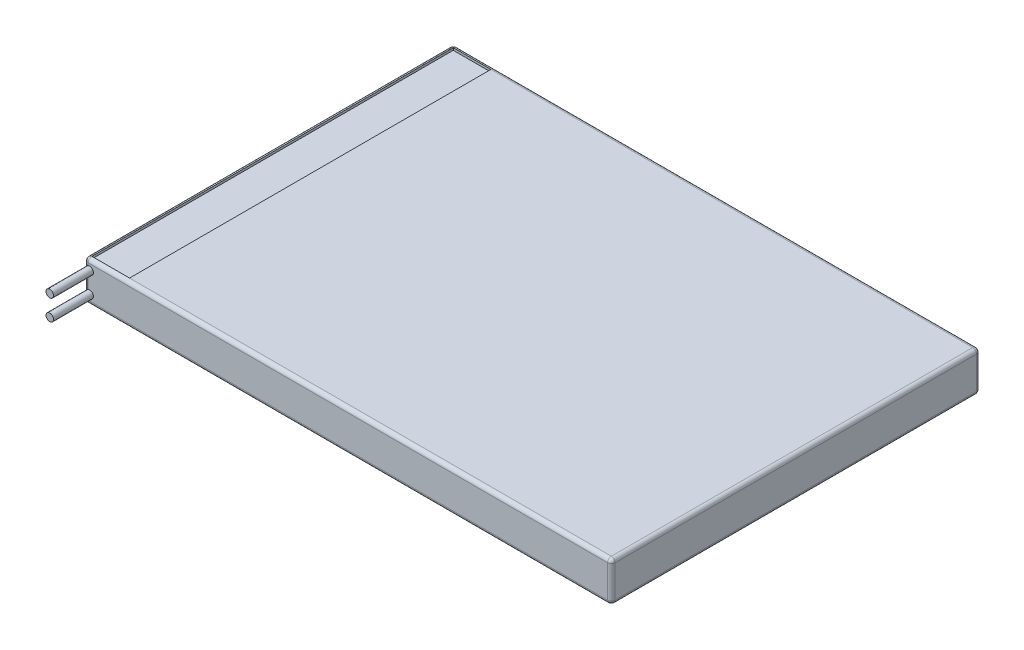
SolidWorks part; units mm, degrees
ref_plane "Front Plane" through (0, 0, 0) normal (0, 0, 1) x (1, 0, 0)
ref_plane "Top Plane" through (0, 0, 0) normal (0, 1, 0) x (1, 0, 0)
ref_plane "Right Plane" through (0, 0, 0) normal (1, 0, 0) x (0, 0, -1)
sketch "Sketch1" plane through (0, 0, 0) normal (0, 1, 0) x (1, 0, 0)
  line L1 (-34.5, -24.5) -> (34.5, -24.5)
  line L2 (-35, -24) -> (-35, 24)
  line L3 (-34.5, 24.5) -> (34.5, 24.5)
  line L4 (35, -24) -> (35, 24)
  line L5 (-35, -24.5) -> (35, 24.5) construction
  line L6 (-35, 24.5) -> (35, -24.5) construction
  arc A0 (-35, -24) -> (-34.5, -24.5) centre (-34.5, -24) ccw
  arc A1 (34.5, -24.5) -> (35, -24) centre (34.5, -24) ccw
  arc A2 (34.5, 24.5) -> (35, 24) centre (34.5, 24) cw
  arc A3 (-35, 24) -> (-34.5, 24.5) centre (-34.5, 24) cw
  point P0 (0, 0)
  dimension "D3" = 0.5
  dimension "D1" = 49
  dimension "D2" = 70
extrude "Boss-Extrude2" add sketch "Sketch1" along normal blind 5.3
sketch "Sketch2" plane through (0, 0, 24.5) normal (0, 0, 1) x (1, 0, 0)
  line L0 (-34.3, 5.3) -> (-34.3, 0) construction
  line L1 (-34.5, 5.3) -> (34.5, 5.3) construction
  line L2 (-34.5, 0) -> (34.5, 0) construction
  line L3 (-34.5, 2.65) -> (-32.7012, 2.65) construction
  line L4 (-34.5, 5.3) -> (-34.5, 0) construction
  circle A0 centre (-34.3, 1.2796) radius 0.5
  circle A1 centre (-34.3, 4.0204) radius 0.5
  dimension "D1" = 1
  dimension "D2" = 0.2
extrude "Boss-Extrude3" add sketch "Sketch2" along normal blind 5.3 and the other way blind 1
fillet "Fillet2" radius 0.5 16 edges at (-34.8536, 5.3, -24.3536) (0, 5.3, -24.5) (34.8536, 5.3, -24.3536) (35, 5.3, 0) (34.8536, 5.3, 24.3536) (0, 5.3, 24.5) (-34.8536, 5.3, 24.3536) (0, 0, 24.5) (34.8536, 0, 24.3536) (35, 0, 0) (34.8536, 0, -24.3536) (0, 0, -24.5) (-34.8536, 0, -24.3536) (-35, 0, 0) (-34.8536, 0, 24.3536) (-35, 5.3, 0)
sketch "Sketch4" plane through (0, 5.3, 0) normal (0, 1, 0) x (1, 0, 0)
  line L0 (-29.5, -24) -> (-29.5, 24)
  line L1 (34.5, 24) -> (-34.5, 24) construction
  line L2 (-29.5, 24) -> (-34.5, 24)
  line L3 (-34.5, 24) -> (-34.5, -24)
  line L4 (-34.5, -24) -> (-29.5, -24)
  line L5 (-34.5, -24) -> (34.5, -24) construction
  dimension "D1" = 5
extrude "Cut-Extrude1" cut sketch "Sketch4" against normal blind 0.3
sketch "Sketch5" plane through (0, 0, 0) normal (0, -1, 0) x (-1, 0, 0)
  line L0 (0, -24) -> (0, 24) construction
  line L1 (-34.5, -24) -> (34.5, -24) construction
  line L2 (34.5, 24) -> (-34.5, 24) construction
